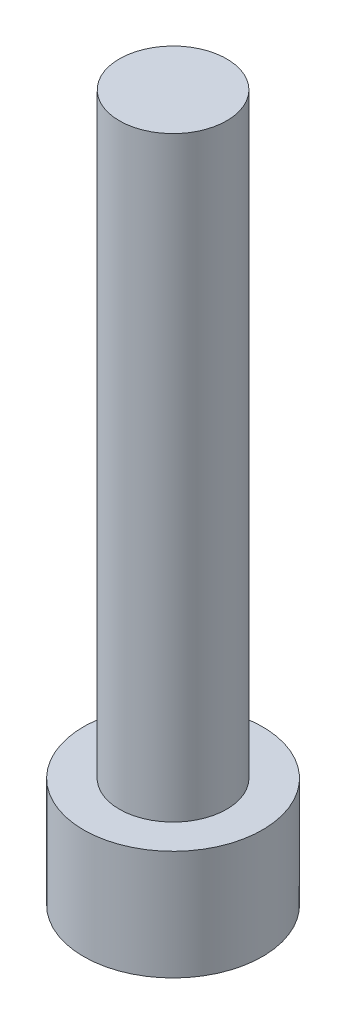
SolidWorks part; units mm, degrees
ref_plane "Front Plane" through (0, 0, 0) normal (0, 0, 1) x (1, 0, 0)
ref_plane "Top Plane" through (0, 0, 0) normal (0, 1, 0) x (1, 0, 0)
ref_plane "Right Plane" through (0, 0, 0) normal (1, 0, 0) x (0, 0, -1)
sketch "Sketch1" plane through (0, 0, 0) normal (0, 1, 0) x (1, 0, 0)
  circle A0 centre (0, 0) radius 2.8575
  dimension "D1" = 5.715
extrude "Boss-Extrude1" add sketch "Sketch1" along normal blind 3.5052
sketch "Sketch2" plane through (0, 0, 0) normal (0, -1, 0) x (1, 0, 0)
  line L1 (1.604, 0) -> (0.802, 1.3891)
  line L2 (0.802, 1.3891) -> (-0.802, 1.3891)
  line L3 (-0.802, 1.3891) -> (-1.604, 0)
  line L4 (-1.604, 0) -> (-0.802, -1.3891)
  line L5 (-0.802, -1.3891) -> (0.802, -1.3891)
  line L6 (0.802, -1.3891) -> (1.604, 0)
  circle A0 centre (0, 0) radius 1.3891 construction
  dimension "D1" = 2.7781
extrude "Cut-Extrude1" cut sketch "Sketch2" against normal blind 1.9558
sketch "Sketch3" plane through (0, 3.5052, 0) normal (0, 1, 0) x (1, 0, 0)
  circle A0 centre (0, 0) radius 1.7145
  dimension "D1" = 3.429
extrude "Boss-Extrude2" add sketch "Sketch3" along normal blind 19.05
